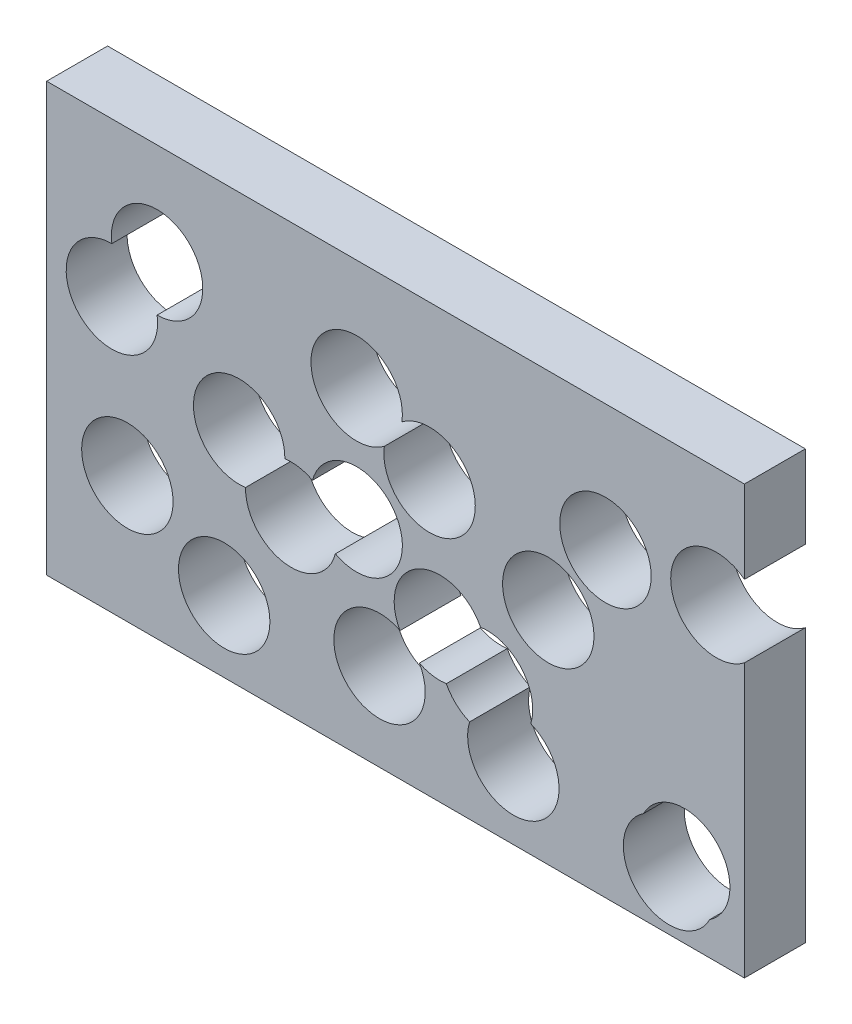
SolidWorks part; units mm, degrees
ref_plane "Přední rovina" through (0, 0, 0) normal (0, 0, 1) x (1, 0, 0)
ref_plane "Vrchní rovina" through (0, 0, 0) normal (0, 1, 0) x (1, 0, 0)
ref_plane "Pravá rovina" through (0, 0, 0) normal (1, 0, 0) x (0, 0, -1)
sketch "Skica1" plane through (0, 0, 0) normal (0, 0, 1) x (1, 0, 0)
  line L1 (-57.2495, 35.101) -> (57.2495, 35.101)
  line L2 (-57.2495, 35.101) -> (-57.2495, -35.101)
  line L3 (-57.2495, -35.101) -> (57.2495, -35.101)
  line L4 (57.2495, 35.101) -> (57.2495, -35.101)
  line L5 (-57.2495, 35.101) -> (57.2495, -35.101) construction
  line L6 (-57.2495, -35.101) -> (57.2495, 35.101) construction
  point P0 (0, 0)
extrude "Přidat vysunutím1" add sketch "Skica1" along normal blind 10
sketch "Skica2" plane through (0, 0, 0) normal (0, 0, -1) x (-1, 0, 0)
  circle A0 centre (-44.8849, -26.2257) radius 7.5
  dimension "D1" = 15
extrude "Odebrat vysunutím1" cut sketch "Skica2" against normal up to next contours A0
sketch "Skica3" plane through (0, 0, 0) normal (0, 0, -1) x (-1, 0, 0)
  point P0 (-34.4532, 14.3334)
  point P1 (2.6254, -20.6901)
  point P2 (46.5466, 9.8642)
  point P3 (-25.0644, 1.1022)
  point P4 (-15.0152, -14.3202)
  point P5 (-5.5881, 9.8642)
  point P6 (6.3781, 16.8846)
  point P7 (28.1166, -23.4153)
  point P8 (17.1165, -6.4428)
  point P9 (25.6587, 1.1022)
  point P10 (6.3781, -1.7363)
  point P11 (-7.2747, -10.3104)
  point P12 (-47.3772, -23.4153)
  point P13 (-52.6556, 15.6118)
  point P14 (-19.3323, -23.4153)
  point P15 (44.0083, -14.3202)
  point P16 (39.1292, 18.4261)
pattern_sketch "Skica-pole1" of "Odebrat vysunutím1" driven by "Skica3"
